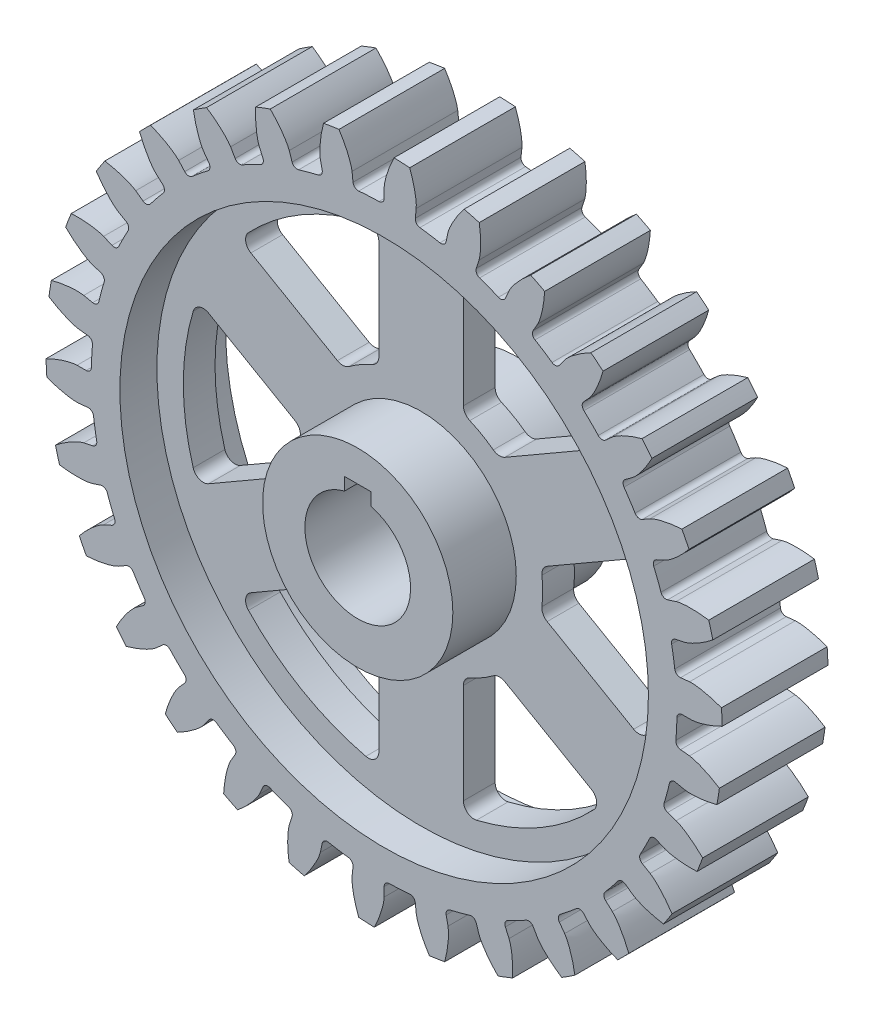
SolidWorks part; units mm, degrees
ref_plane "Front Plane" through (0, 0, 0) normal (0, 0, 1) x (1, 0, 0)
ref_plane "Top Plane" through (0, 0, 0) normal (0, 1, 0) x (1, 0, 0)
ref_plane "Right Plane" through (0, 0, 0) normal (1, 0, 0) x (0, 0, -1)
sketch "Sketch1" plane through (0, 0, 0) normal (1, 0, 0) x (0, 0, -1)
  line L0 (0, 0) -> (19.05, 0)
  line L1 (20.955, 0) -> (-20.955, 0) construction
  line L2 (19.05, 0) -> (19.05, 22.86)
  line L3 (19.05, 22.86) -> (3.81, 22.86)
  line L4 (3.81, 22.86) -> (3.81, 63.5)
  line L5 (3.81, 63.5) -> (12.7, 63.5)
  line L6 (12.7, 63.5) -> (12.7, 70.358)
  line L7 (12.7, 70.358) -> (-12.7, 70.358)
  line L8 (0, 38.6969) -> (0, -38.6969) construction
  line L9 (0, 0) -> (0, 86.2133) construction
  line L10 (-19.05, 0) -> (-19.05, 22.86)
  line L11 (-19.05, 22.86) -> (-3.81, 22.86)
  line L12 (-3.81, 22.86) -> (-3.81, 63.5)
  line L13 (-3.81, 63.5) -> (-12.7, 63.5)
  line L14 (-12.7, 63.5) -> (-12.7, 70.358)
  line L15 (-19.05, 0) -> (0, 0)
  point P21 (0, 70.358)
  dimension "D1" = 19.05
  dimension "D2" = 22.86
  dimension "D3" = 3.81
  dimension "D4" = 70.358
  dimension "D5" = 63.5
  dimension "D6" = 12.7
ref_axis "Axis1" through (0, 0, 20.955) along (0, 0, -1)
revolve "Revolve1" add sketch "Sketch1" angle 360 about L15
sketch "Sketch2" plane through (0, 0, 0) normal (0, 0, 1) x (1, 0, 0)
  line L0 (73.787, 0) -> (70.358, 0)
  line L1 (0, 0) -> (81.1686, 4.2539) construction
  line L2 (73.3828, 7.7128) -> (69.9726, 7.3544)
  arc A0 (81.2453, 2.3735) -> (81.0484, 6.132) centre (0, 0) ccw
  circle A1 centre (0, 0) radius 70.358 construction
  arc A2 (70.358, 0) -> (69.9726, 7.3544) centre (0, 0) ccw
  spline S0 degree 4 poles (73.787, 0) (73.8416, 0.0012) (73.9944, 0.008) (74.2828, 0.0349) (74.7515, 0.0989) (75.345, 0.2096) (76.1065, 0.3861) (76.9949, 0.6365) (77.9608, 0.9559) (79.2577, 1.449) (80.5285, 2.0097) (81.7724, 2.6274) (83.1972, 3.4098) (84.592, 4.2449) (86.1811, 5.2931) (87.9419, 6.5808) (89.6733, 7.9733) (91.3432, 9.4391) (92.7509, 10.7796) (93.9201, 11.967) (94.8691, 12.9798) (95.614, 13.8045) (96.5255, 14.8499) (97.4145, 15.9197) (98.1892, 16.8948) (98.8659, 17.7823) (99.359, 18.4422) (99.8613, 19.1329) (100.322, 19.7792) (100.825, 20.5115) (101.2452, 21.1308) (101.7679, 21.9265) (102.1191, 22.4721) (102.7345, 23.4529) (103.1421, 24.1299) (103.5488, 24.8103) (103.7468, 25.157) (103.8765, 25.3798) knots 0 0 0 0 0 0.005377 0.015084 0.028532 0.04661 0.064855 0.092111 0.119476 0.146842 0.201575 0.228941 0.256307 0.307035 0.361767 0.4165 0.471232 0.525964 0.580697 0.608063 0.635429 0.662795 0.690161 0.744894 0.77226 0.785943 0.799626 0.826992 0.854358 0.868042 0.881725 0.909091 0.931818 0.954545 0.977273 1 1 1 1 1 construction
  spline S1 degree 4 poles (73.787, 0) (73.8416, 0.0012) (73.9944, 0.008) (74.2828, 0.0349) (74.7515, 0.0989) (75.345, 0.2096) (76.1065, 0.3861) (76.9949, 0.6365) (77.9608, 0.9559) (79.1859, 1.4218) (80.1337, 1.8358) (80.817, 2.1602) (81.2453, 2.3735) knots 0 0 0 0 0 0.005377 0.015084 0.028532 0.04661 0.064855 0.092111 0.119476 0.146842 0.194009 0.194009 0.194009 0.194009 0.194009
  spline S2 degree 4 poles (73.3828, 7.7128) (73.4372, 7.7174) (73.5899, 7.7266) (73.8795, 7.7299) (74.3523, 7.7153) (74.9541, 7.6672) (75.7299, 7.5713) (76.6397, 7.4152) (77.6336, 7.1984) (78.9008, 6.8632) (79.8866, 6.5505) (80.6, 6.2993) (81.0484, 6.132) knots 0 0 0 0 0 0.005377 0.015084 0.028532 0.04661 0.064855 0.092111 0.119476 0.146842 0.194009 0.194009 0.194009 0.194009 0.194009
  dimension "D1" = 3
extrude "Boss-Extrude1" add sketch "Sketch2" along normal up to surface and the other way up to surface
fillet "Fillet1" radius 1.27 2 edges at (70.358, 0, 0) (69.9726, 7.3544, 0)
pattern_circular "CirPattern1" count 30 over 360 about axis through (0, 0, 20.955) along (0, 0, -1) of "Boss-Extrude1", "Fillet1"
sketch "Sketch3" plane through (0, 0, 0) normal (0, 0, 1) x (1, 0, 0)
  line L2 (-3.175, 12.2967) -> (-3.175, 15.3447)
  line L3 (-3.175, 15.3447) -> (3.175, 15.3447)
  line L4 (3.175, 12.2967) -> (3.175, 15.3447)
  line L5 (0, -20.955) -> (0, 20.955) construction
  arc A0 (-3.175, 12.2967) -> (3.175, 12.2967) centre (0, 0) ccw
  dimension "D1" = 3.175
  dimension "D4" = 12.7
  dimension "D2" = 6.35
  dimension "D3" = 3.048
extrude "Cut-Extrude1" cut sketch "Sketch3" against normal through all both and the other way through all
sketch "Sketch4" plane through (0, 0, 0) normal (0, 0, 1) x (1, 0, 0)
  line L0 (0, 0) -> (112.4903, 64.9463) construction
  line L1 (20.955, 0) -> (-20.955, 0) construction
  line L3 (18.6371, 22.4919) -> (43.625, 36.9186)
  line L4 (10.16, 56.2396) -> (10.16, 27.3861)
  arc A0 (43.625, 36.9186) -> (10.16, 56.2396) centre (0, 0) ccw
  arc A1 (18.6371, 22.4919) -> (10.16, 27.3861) centre (0, 0) ccw
  dimension "D1" = 57.15
  dimension "D2" = 29.21
  dimension "D3" = 10.16
  dimension "D4" = 30
  dimension "D5" = 10.16
extrude "Cut-Extrude3" cut sketch "Sketch4" against normal through all both and the other way through all contours A0 L4 A1 L3
fillet "Fillet3" radius 2.54 4 edges at (43.625, 36.9186, 0) (18.6371, 22.4919, 0) (10.16, 27.3861, 0) (10.16, 56.2396, 0)
pattern_circular "CirPattern4" count 6 over 360 about axis through (0, 0, 0) along (0, 0, 1) of "Fillet3", "Cut-Extrude3"
